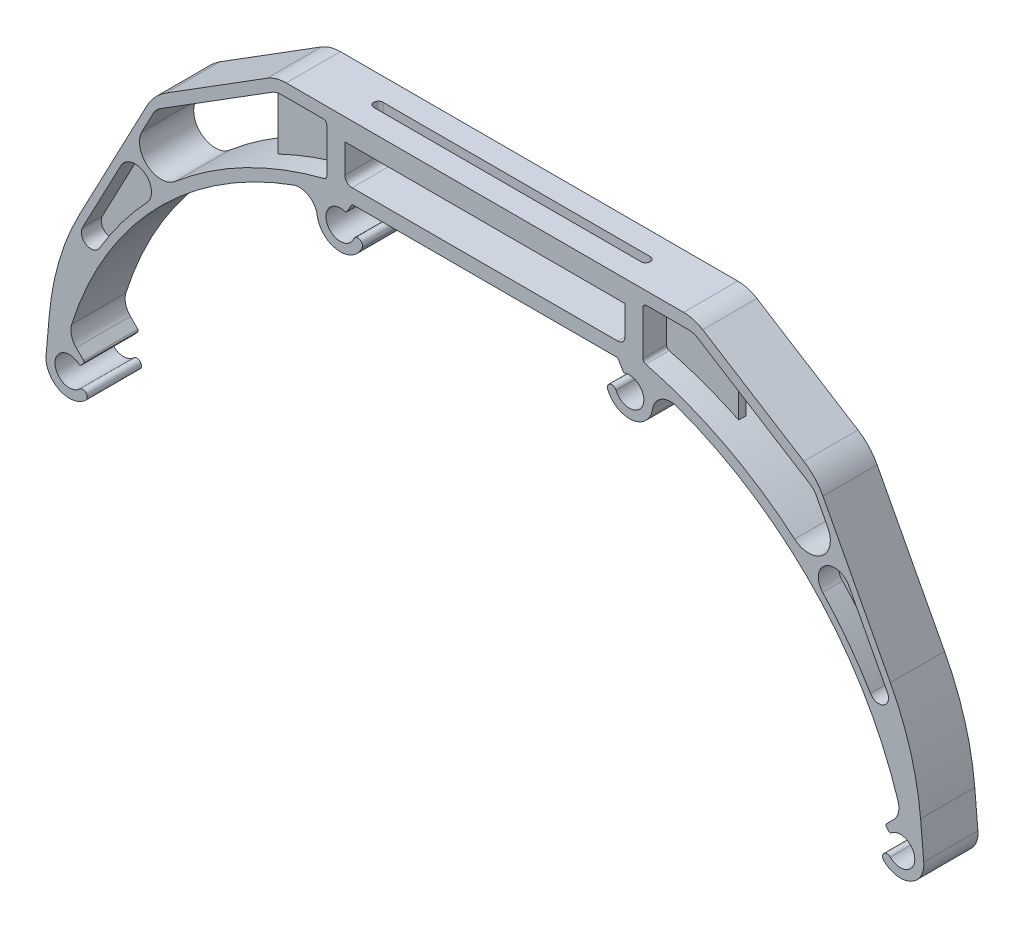
SolidWorks part; units mm, degrees
ref_plane "前视基准面" through (0, 0, 0) normal (0, 0, 1) x (1, 0, 0)
ref_plane "上视基准面" through (0, 0, 0) normal (0, 1, 0) x (1, 0, 0)
ref_plane "右视基准面" through (0, 0, 0) normal (1, 0, 0) x (0, 0, -1)
other "Configuration Table"
sketch "草图3" plane through (0, 0, 0) normal (0, 0, 1) x (1, 0, 0)
  line L1 (3.2788, 3.1231) -> (3.9216, 3.8891)
  line L2 (-171.2343, 0) -> (-157.0965, 0) construction
  line L3 (-2.777, -5.8769) -> (342.8473, -5.8769) construction
  line L4 (115, 344.437) -> (115, -146.1908) construction
  line L5 (21.4262, 74.3563) -> (2.769, 38.974)
  line L6 (60, 99.1231) -> (170, 99.1231)
  line L7 (76.7911, 76.6633) -> (78.067, 78.8731)
  line L8 (-5.6037, 10.5285) -> (-6.4753, 0.5665)
  line L9 (75, 79.1231) -> (155, 79.1231)
  line L10 (54.6889, 97.5961) -> (26.7279, 80.0694)
  line L11 (3.8921, 4.5641) -> (1.8686, 6.5876)
  line L12 (401.2343, 0) -> (387.0965, 0) construction
  line L13 (226.1079, 4.5641) -> (228.1314, 6.5876)
  line L14 (175.3111, 97.5961) -> (203.2721, 80.0694)
  line L15 (235.6037, 10.5285) -> (236.4753, 0.5665)
  line L16 (208.5738, 74.3563) -> (227.231, 38.974)
  line L19 (153.2089, 76.6633) -> (151.933, 78.8731)
  line L20 (226.7212, 3.1231) -> (226.0784, 3.8891)
  arc A0 (-6.4753, 0.5665) -> (4.5491, -4.6429) centre (0, 0) ccw
  arc A1 (2.574, 3.0618) -> (2.7994, -2.8571) centre (0, 0) ccw
  arc A2 (3.2788, 3.1231) -> (2.574, 3.0618) centre (2.8958, 3.4445) cw
  arc A6 (72.6638, 78.8464) -> (0.6346, 11.6236) centre (96.0254, -18.3865) ccw
  arc A7 (21.4262, 74.3563) -> (26.7279, 80.0694) centre (34.6946, 67.3599) cw
  arc A8 (2.769, 38.974) -> (-5.6037, 10.5285) centre (69.1109, 3.9918) ccw
  arc A9 (1.8686, 6.5876) -> (0.6346, 11.6236) centre (5.4042, 10.1231) cw
  arc A10 (72.6638, 78.8464) -> (75, 79.1231) centre (75, 69.1231) cw
  arc A11 (54.6889, 97.5961) -> (60, 99.1231) centre (60, 89.1231) cw
  arc A15 (68.5718, 71.6595) -> (61.9219, 75.6185) centre (63.6271, 70.9183) ccw
  arc A16 (68.5718, 71.6595) -> (81.0099, 70.1469) centre (75, 72.6231) ccw
  arc A17 (161.4282, 71.6595) -> (168.0781, 75.6185) centre (166.3729, 70.9183) cw
  arc A18 (151.933, 78.8731) -> (151.5, 79.1231) centre (151.5, 78.6231) ccw
  arc A19 (153.2089, 76.6633) -> (153.7928, 76.4366) centre (153.6419, 76.9133) ccw
  arc A20 (175.3111, 97.5961) -> (170, 99.1231) centre (170, 89.1231) ccw
  arc A21 (157.3362, 78.8464) -> (155, 79.1231) centre (155, 69.1231) ccw
  arc A22 (228.1314, 6.5876) -> (229.3654, 11.6236) centre (224.5958, 10.1231) ccw
  arc A23 (227.231, 38.974) -> (235.6037, 10.5285) centre (160.8891, 3.9918) cw
  arc A24 (208.5738, 74.3563) -> (203.2721, 80.0694) centre (195.3054, 67.3599) ccw
  arc A25 (157.3362, 78.8464) -> (229.3654, 11.6236) centre (133.9746, -18.3865) cw
  arc A30 (227.426, 3.0618) -> (227.2006, -2.8571) centre (230, 0) cw
  arc A31 (236.4753, 0.5665) -> (225.4509, -4.6429) centre (230, 0) cw
  arc A32 (153.7928, 76.4366) -> (151.3016, 71.0993) centre (155, 72.6231) cw
  arc A33 (148.9901, 70.1469) -> (151.3016, 71.0993) centre (150.1459, 70.6231) cw
  arc A34 (2.7994, -2.8571) -> (4.5491, -4.6429) centre (3.6742, -3.75) cw
  arc A35 (3.8921, 4.5641) -> (3.9216, 3.8891) centre (3.5386, 4.2105) cw
  arc A36 (227.2006, -2.8571) -> (225.4509, -4.6429) centre (226.3258, -3.75) ccw
  arc A37 (226.7212, 3.1231) -> (227.426, 3.0618) centre (227.1042, 3.4445) ccw
  arc A38 (226.1079, 4.5641) -> (226.0784, 3.8891) centre (226.4614, 4.2105) ccw
  arc A40 (161.4282, 71.6595) -> (148.9901, 70.1469) centre (155, 72.6231) cw
  arc A41 (76.2072, 76.4366) -> (78.6984, 71.0993) centre (75, 72.6231) ccw
  arc A42 (81.0099, 70.1469) -> (78.6984, 71.0993) centre (79.8541, 70.6231) ccw
  arc A43 (78.067, 78.8731) -> (78.5, 79.1231) centre (78.5, 78.6231) cw
  arc A44 (76.7911, 76.6633) -> (76.2072, 76.4366) centre (76.3581, 76.9133) cw
  point P16 (-164.3242, -93.5575)
  point P19 (115, 79.1231)
  point P36 (115, 99.1231)
  point P49 (0, 0)
  point P84 (80.629, 76.1303)
  point P85 (82.8999, 78.3949)
  point P89 (57.3851, -101.421)
  point P90 (55.9664, -101.9082)
  point P91 (29.5191, -16.6258)
  point P92 (394.3242, -93.5575)
  point P93 (59.2317, -96.6217)
  point P97 (0, 0)
  point P99 (77.8868, 78.3949)
  point P100 (75.8111, 76.1017)
  dimension "D1" = 8
  dimension "D2" = 13
  dimension "D4" = 0.5
  dimension "D5" = 3.75
  dimension "D6" = 10
  dimension "D13" = 15
  dimension "D18" = 75
  dimension "D19" = 100
  dimension "D20" = 5
  dimension "D22" = 10
  dimension "D23" = 13
  dimension "D24" = 8
  dimension "D28" = 3.5
  dimension "D29" = 0.5
  dimension "D26" = 60
  dimension "D27" = 0.5
  dimension "D32" = 0.5
  dimension "D3" = 50
  dimension "D7" = 105
  dimension "D8" = 20
  dimension "D9" = 110
  dimension "D10" = 80
  dimension "D11" = 85
  dimension "D12" = 10
  dimension "D14" = 33
  dimension "D15" = 115
  dimension "D16" = 45
  dimension "D17" = 1
  dimension "D21" = 16
  dimension "D25" = 2
  dimension "D30" = 40
  dimension "D31" = 9
extrude "凸台-拉伸7" add sketch "草图3" along normal blind 15 contours L13 A38 L20 A37 A30 A36 A31 L15 A23 L16 A24 L14 A20 L6 A11 L10 A7 L5 A8 L8 A0 A34 A1 A2 L1 A35 L11 A9 A6 A10 L9 A21 A25 A22 | A40 A17 A25 A21 L9 A18 L19 A19 A32 A33 | A44 L7 A43 L9 A10 A6 A15 A16 A42 A41
sketch "草图6" plane through (0, 0, 15) normal (0, 0, 1) x (1, 0, 0)
  line L0 (56.0188, 94.8891) -> (25.0369, 75.4688)
  line L1 (23.2697, 73.5644) -> (20.0752, 67.5064)
  line L2 (71.2369, 82.432) -> (71.2369, 94.6526)
  line L3 (70.2369, 95.6526) -> (58.6744, 95.6526)
  line L4 (54.6889, 97.5961) -> (26.7279, 80.0694) construction
  line L5 (21.4262, 74.3563) -> (2.769, 38.974) construction
  line L6 (51.2369, 91.8916) -> (51.2369, 74.4374)
  line L7 (115, 99.1231) -> (115, -1.0858) construction
  line L8 (60, 99.1231) -> (170, 99.1231) construction
  line L9 (178.7631, 91.8916) -> (178.7631, 74.4374)
  line L10 (159.7631, 95.6526) -> (171.3256, 95.6526)
  line L11 (158.7631, 82.432) -> (158.7631, 94.6526)
  line L12 (206.7303, 73.5644) -> (209.9248, 67.5064)
  line L13 (173.9812, 94.8891) -> (204.9631, 75.4688)
  arc A0 (20.0752, 67.5064) -> (29.2689, 60.1365) centre (25.3826, 64.7078) ccw
  arc A1 (29.2689, 60.1365) -> (70.4847, 81.4632) centre (96.0254, -18.3865) cw
  arc A4 (61.9219, 75.6185) -> (0.6346, 11.6236) centre (96.0254, -18.3865) ccw construction
  arc A6 (60, 99.1231) -> (54.6889, 97.5961) centre (60, 89.1231) ccw construction
  arc A7 (25.0369, 75.4688) -> (23.2697, 73.5644) centre (27.6925, 71.2323) ccw
  arc A8 (56.0188, 94.8891) -> (58.6744, 95.6526) centre (58.6744, 90.6526) cw
  arc A9 (70.4847, 81.4632) -> (71.2369, 82.432) centre (70.2369, 82.432) ccw
  arc A10 (71.2369, 94.6526) -> (70.2369, 95.6526) centre (70.2369, 94.6526) ccw
  arc A11 (158.7631, 94.6526) -> (159.7631, 95.6526) centre (159.7631, 94.6526) cw
  arc A12 (159.5153, 81.4632) -> (158.7631, 82.432) centre (159.7631, 82.432) cw
  arc A13 (173.9812, 94.8891) -> (171.3256, 95.6526) centre (171.3256, 90.6526) ccw
  arc A14 (204.9631, 75.4688) -> (206.7303, 73.5644) centre (202.3075, 71.2323) cw
  arc A15 (200.7311, 60.1365) -> (159.5153, 81.4632) centre (133.9746, -18.3865) ccw
  arc A16 (209.9248, 67.5064) -> (200.7311, 60.1365) centre (204.6174, 64.7078) cw
  point P26 (57.2369, 98.7338)
  point P27 (57.2369, 95.6526)
  point P30 (71.2369, 81.6526)
  point P33 (71.2369, 95.6526)
  point P54 (158.7631, 95.6526)
  point P55 (158.7631, 81.6526)
  point P56 (172.7631, 95.6526)
  dimension "D2" = 14
  dimension "D3" = 6
  dimension "D6" = 5
  dimension "D7" = 1
  dimension "D1" = 3
  dimension "D4" = 2
  dimension "D5" = 14
  dimension "D8" = 20
extrude "切除-拉伸1" cut sketch "草图6" against normal through all contours L2 A10 L3 A8 L0 L6 A1 A9 | L0 A7 L1 A0 A1 L6 | A15 L9 L13 A13 L10 A11 L11 A12 | A16 L12 A14 L13 L9 A15
ref_plane "基准面1" through (0, 0, 7.5) normal (0, 0, 1) x (1, 0, 0)
sketch "草图7" plane through (0, 0, 7.5) normal (0, 0, 1) x (1, 0, 0)
  line L0 (51.2369, 91.8916) -> (51.2369, 74.4374) construction
  line L1 (51.2369, 91.8916) -> (51.2369, 74.4374)
rib "筋4" sketch "草图7" sketch "草图7" thickness 2 extrusion direction parallel to sketch draft on no parameters "D1"=2
sketch "草图8" plane through (0, 0, 7.5) normal (0, 0, 1) x (1, 0, 0)
  line L0 (178.7631, 91.8916) -> (178.7631, 74.4374) construction
  line L1 (178.7631, 91.8916) -> (178.7631, 74.4374)
rib "筋5" sketch "草图8" sketch "草图8" thickness 2 extrusion direction parallel to sketch draft on no parameters "D1"=2
sketch "草图9" plane through (0, 0, 15) normal (0, 0, 1) x (1, 0, 0)
  line L0 (115, 93.1231) -> (115, 67.4778) construction
  line L1 (76.2369, 93.1231) -> (153.7631, 93.1231)
  line L2 (76.2369, 93.1231) -> (76.2369, 85.1231)
  line L3 (78.2369, 83.1231) -> (151.7631, 83.1231)
  line L4 (153.7631, 93.1231) -> (153.7631, 85.1231)
  line L5 (60, 99.1231) -> (170, 99.1231) construction
  line L6 (78.5, 79.1231) -> (151.5, 79.1231) construction
  line L7 (158.7631, 94.6526) -> (158.7631, 82.432) construction
  line L8 (71.2369, 82.432) -> (71.2369, 94.6526) construction
  arc A0 (151.7631, 83.1231) -> (153.7631, 85.1231) centre (151.7631, 85.1231) ccw
  arc A1 (76.2369, 85.1231) -> (78.2369, 83.1231) centre (78.2369, 85.1231) ccw
  dimension "D5" = 2
  dimension "D1" = 6
  dimension "D2" = 4
  dimension "D3" = 5
  dimension "D4" = 5
extrude "切除-拉伸2" cut sketch "草图9" against normal through all
sketch "草图10" plane through (0, 99.1231, 0) normal (0, 1, 0) x (1, 0, 0)
  line L0 (175.3111, -15) -> (175.3111, 0) construction
  line L1 (78, -6.25) -> (152, -6.25)
  line L3 (78, -8.75) -> (152, -8.75)
  line L5 (78.0013, -6.25) -> (151.9987, -8.75) construction
  line L6 (78, -8.75) -> (152, -6.25) construction
  line L7 (170, -15) -> (170, 0) construction
  line L8 (60, -15) -> (170, -15) construction
  arc A0 (78.0831, -6.2528) -> (78.0844, -8.7471) centre (78, -7.5) ccw
  arc A1 (151.9169, -8.7472) -> (151.9156, -6.2529) centre (152, -7.5) ccw
  point P0 (115, -7.5)
  point P3 (115, -8.75)
  point P4 (0, 0)
  point P9 (175.3111, -7.5)
  point P12 (170, -7.5)
  point P15 (115, -15)
  point P21 (115, -6.25)
  dimension "D1" = 74
  dimension "D2" = 2.5
extrude "切除-拉伸3" cut sketch "草图10" against normal blind 10
sketch "草图11" plane through (0, 0, 15) normal (0, 0, 1) x (1, 0, 0)
  line L0 (14.2221, 56.4063) -> (3.5956, 36.2537)
  line L1 (21.4262, 74.3563) -> (2.769, 38.974) construction
  line L2 (115, 79.1231) -> (115, -31.2667) construction
  line L3 (78.5, 79.1231) -> (151.5, 79.1231) construction
  line L4 (215.7779, 56.4063) -> (226.4044, 36.2537)
  arc A0 (3.5956, 36.2537) -> (8.2851, 33.6293) centre (5.9731, 35) ccw
  arc A1 (21.4855, 51.2396) -> (14.2221, 56.4063) centre (18.1995, 54.309) ccw
  arc A2 (21.4855, 51.2396) -> (8.2851, 33.6293) centre (96.0254, -18.3865) ccw
  arc A3 (61.9219, 75.6185) -> (0.6346, 11.6236) centre (96.0254, -18.3865) ccw construction
  arc A4 (26.7279, 80.0694) -> (21.4262, 74.3563) centre (34.6946, 67.3599) ccw construction
  arc A5 (208.5145, 51.2396) -> (221.7149, 33.6293) centre (133.9746, -18.3865) cw
  arc A6 (208.5145, 51.2396) -> (215.7779, 56.4063) centre (211.8005, 54.309) cw
  arc A7 (226.4044, 36.2537) -> (221.7149, 33.6293) centre (224.0269, 35) cw
  point P15 (23.6995, 77.5632)
  dimension "D1" = 2
  dimension "D3" = 5.5
  dimension "D2" = 2
  dimension "D4" = 35
extrude "切除-拉伸4" cut sketch "草图11" against normal through all
sketch "草图12" plane through (0, 0, 7.5) normal (0, 0, 1) x (1, 0, 0)
  line L0 (215.7779, 56.4063) -> (226.4044, 36.2537) construction
  line L1 (14.2221, 56.4063) -> (3.5956, 36.2537) construction
  line L2 (215.7779, 56.4063) -> (226.4044, 36.2537)
  line L3 (14.2221, 56.4063) -> (3.5956, 36.2537)
  arc A0 (221.7149, 33.6293) -> (226.4044, 36.2537) centre (224.0269, 35) ccw construction
  arc A1 (221.7149, 33.6293) -> (208.5145, 51.2396) centre (133.9746, -18.3865) ccw construction
  arc A2 (215.7779, 56.4063) -> (208.5145, 51.2396) centre (211.8005, 54.309) ccw construction
  arc A3 (3.5956, 36.2537) -> (8.2851, 33.6293) centre (5.9731, 35) ccw construction
  arc A4 (21.4855, 51.2396) -> (8.2851, 33.6293) centre (96.0254, -18.3865) ccw construction
  arc A5 (21.4855, 51.2396) -> (14.2221, 56.4063) centre (18.1995, 54.309) ccw construction
  arc A6 (221.7149, 33.6293) -> (226.4044, 36.2537) centre (224.0269, 35) ccw
  arc A7 (221.7149, 33.6293) -> (208.5145, 51.2396) centre (133.9746, -18.3865) ccw
  arc A8 (215.7779, 56.4063) -> (208.5145, 51.2396) centre (211.8005, 54.309) ccw
  arc A9 (3.5956, 36.2537) -> (8.2851, 33.6293) centre (5.9731, 35) ccw
  arc A10 (21.4855, 51.2396) -> (8.2851, 33.6293) centre (96.0254, -18.3865) ccw
  arc A11 (21.4855, 51.2396) -> (14.2221, 56.4063) centre (18.1995, 54.309) ccw
extrude "凸台-拉伸8" add sketch "草图12" along normal mid plane 4 contours L3 A9 A10 A11 | A6 L2 A8 A7
